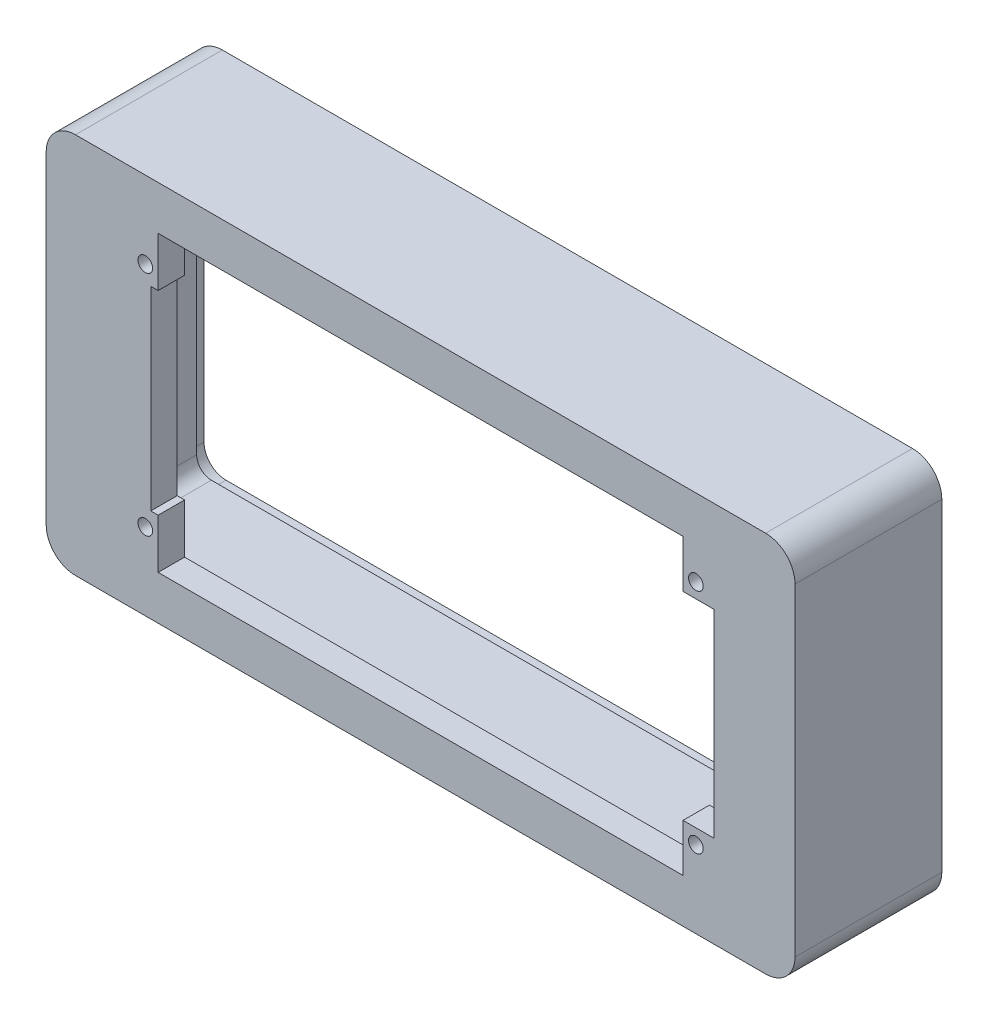
SolidWorks part; units mm, degrees
ref_plane "Plan de face" through (0, 0, 0) normal (0, 0, 1) x (1, 0, 0)
ref_plane "Plan de dessus" through (0, 0, 0) normal (0, 1, 0) x (1, 0, 0)
ref_plane "Plan de droite" through (0, 0, 0) normal (1, 0, 0) x (0, 0, -1)
sketch "Esquisse1" plane through (0, 0, 0) normal (0, 0, 1) x (1, 0, 0)
  line L1 (0, 0) -> (90, 0)
  line L2 (0, 0) -> (0, 40)
  line L3 (0, 40) -> (90, 40)
  line L4 (90, 0) -> (90, 40)
  dimension "D1" = 90
  dimension "D2" = 40
extrude "Extru.-Mince1" add sketch "Esquisse1" along normal blind 3.6 thin
sketch "Esquisse2" plane through (0, 0, 0) normal (0, 0, 1) x (1, 0, 0)
  line L0 (0, 40) -> (0, 0) construction
  line L1 (0, 40) -> (9.25, 40)
  line L2 (0, 40) -> (0, 0)
  line L3 (0, 0) -> (9.25, 0)
  line L4 (9.25, 40) -> (9.25, 0)
  line L5 (-43.2536, 20) -> (124.6424, 20) construction
  line L6 (90, 40) -> (0, 40) construction
  line L7 (0, 0) -> (90, 0) construction
  line L8 (90, 40) -> (90, 0)
  line L9 (90, 0) -> (90, 40) construction
  line L10 (90, 0) -> (80.75, 0)
  line L11 (0, 0) -> (90, 0) construction
  line L12 (80.75, 0) -> (80.75, 6.5)
  line L13 (80.75, 6.5) -> (85, 6.5)
  line L14 (85, 6.5) -> (85, 33.5)
  line L15 (85, 33.5) -> (80.75, 33.5)
  line L16 (80.75, 33.5) -> (80.75, 40)
  line L17 (80.75, 40) -> (90, 40)
  dimension "D1" = 9.25
  dimension "D2" = 40
  dimension "D3" = 9.25
  dimension "D4" = 27
  dimension "D5" = 5
extrude "Boss.-Extru.1" add sketch "Esquisse2" along normal blind 3.6
sketch "Esquisse3" plane through (0, 0, 0) normal (0, 0, 1) x (1, 0, 0)
  line L0 (7.5, 35.5) -> (7.5, 4.5) construction
  line L1 (7.5, 4.5) -> (82.5, 4.5) construction
  line L3 (-6, 46) -> (-6, -6) construction
  line L4 (96, 46) -> (-6, 46) construction
  line L5 (115.7343, 20) -> (-33.996, 20) construction
  line L6 (12.5477, 33.25) -> (8.25, 33.25)
  line L7 (12.5477, 33.25) -> (12.5477, 6.75)
  line L8 (12.5477, 6.75) -> (8.25, 6.75)
  line L9 (8.25, 33.25) -> (8.25, 6.75)
  line L10 (-6, -6) -> (96, -6) construction
  line L11 (9.25, 0) -> (9.25, 40) construction
  circle A0 centre (7.5, 35.5) radius 1
  circle A1 centre (7.5, 4.5) radius 1
  circle A2 centre (82.5, 35.5) radius 1
  circle A3 centre (82.5, 4.5) radius 1
  dimension "D1" = 2
  dimension "D2" = 31
  dimension "D3" = 31
  dimension "D4" = 75
  dimension "D5" = 75
  dimension "D6" = 13.5
  dimension "D7" = 10.5
  dimension "D8" = 26.5
  dimension "D9" = 1
extrude "Enlèv. mat.-Extru.1" cut sketch "Esquisse3" along normal blind 3.6
ref_plane "Plan4" through (0, 0, 3.6) normal (0, 0, 1) x (1, 0, 0)
sketch "Esquisse5" plane through (0, 0, 3.6) normal (0, 0, 1) x (1, 0, 0)
  line L1 (96, 46) -> (-6, 46)
  line L2 (96, 46) -> (96, -6)
  line L3 (96, -6) -> (-6, -6)
  line L4 (-6, 46) -> (-6, -6)
extrude "Extru.-Mince2" add sketch "Esquisse5" against normal blind 20 thin thin type one direction reverse wall 2.5
fillet "Congé1" radius 4 4 edges at (96, -6, -6.4) (-6, -6, -6.4) (-6, 46, -6.4) (96, 46, -6.4)
fillet "Congé2" radius 2 8 edges at (-3.5, 20, 0) (45, -3.5, 0) (93.5, 20, 0) (45, 43.5, 0) (93.5, -3.5, -8.2) (93.5, 43.5, -8.2) (-3.5, -3.5, -8.2) (-3.5, 43.5, -8.2)
sketch "Esquisse6" plane through (0, 0, -16.4) normal (0, 0, -1) x (-1, 0, 0)
  line L5 (3.5, -1.5) -> (3.5, 41.5)
  line L6 (-91.5, -3.5) -> (1.5, -3.5)
  line L7 (-93.5, 41.5) -> (-93.5, -1.5)
  line L16 (1.5, 43.5) -> (-91.5, 43.5)
  line L17 (3.5, -1.5) -> (3.5, 41.5)
  line L18 (-91.5, -3.5) -> (1.5, -3.5)
  line L19 (-93.5, 41.5) -> (-93.5, -1.5)
  line L20 (1.5, 43.5) -> (-91.5, 43.5)
  arc A4 (1.5, -3.5) -> (3.5, -1.5) centre (1.5, -1.5) ccw
  arc A5 (-93.5, -1.5) -> (-91.5, -3.5) centre (-91.5, -1.5) ccw
  arc A6 (-91.5, 43.5) -> (-93.5, 41.5) centre (-91.5, 41.5) ccw
  arc A7 (3.5, 41.5) -> (1.5, 43.5) centre (1.5, 41.5) ccw
  arc A16 (1.5, -3.5) -> (3.5, -1.5) centre (1.5, -1.5) ccw
  arc A17 (-93.5, -1.5) -> (-91.5, -3.5) centre (-91.5, -1.5) ccw
  arc A18 (-91.5, 43.5) -> (-93.5, 41.5) centre (-91.5, 41.5) ccw
  arc A19 (3.5, 41.5) -> (1.5, 43.5) centre (1.5, 41.5) ccw
  dimension "D1" = 0
extrude "Enlèv. de mat.-Extru.-Mince1" cut sketch "Esquisse6" against normal blind 2 thin
ref_plane "Plan5" through (0, 0, -16.4) normal (0, 0, -1) x (-1, 0, 0)
